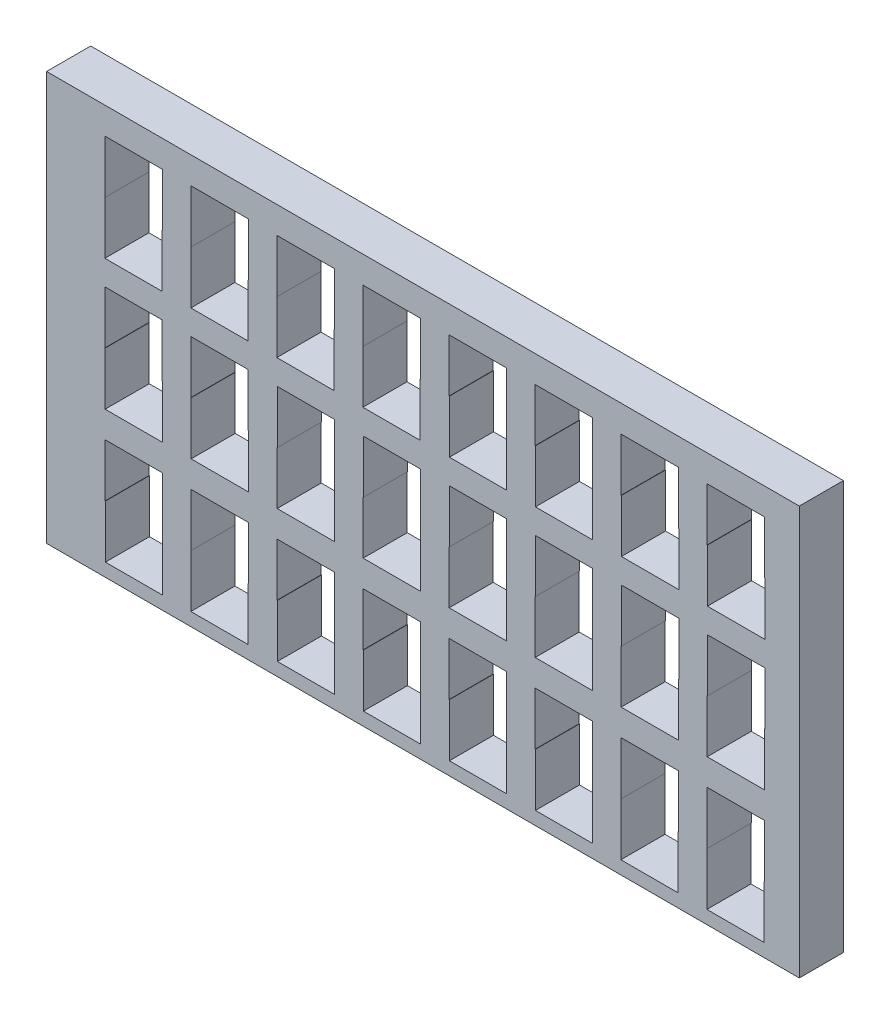
SolidWorks part; units mm, degrees
ref_plane "Front Plane" through (0, 0, 0) normal (0, 0, 1) x (1, 0, 0)
ref_plane "Top Plane" through (0, 0, 0) normal (0, 1, 0) x (1, 0, 0)
ref_plane "Right Plane" through (0, 0, 0) normal (1, 0, 0) x (0, 0, -1)
sketch "Sketch1" plane through (0, 0, 0) normal (0, 0, 1) x (1, 0, 0)
  line L25 (68.6659, 68.7531) -> (68.6659, 56.7531)
  line L26 (68.6659, 68.7531) -> (55.6659, 68.7531)
  line L27 (55.6659, 68.7531) -> (55.6659, 56.7531)
  line L29 (88.1659, 68.7531) -> (88.1659, 56.7531)
  line L30 (88.1659, 68.7531) -> (75.1659, 68.7531)
  line L31 (75.1659, 68.7531) -> (75.1659, 56.7531)
  line L33 (107.6659, 68.7531) -> (107.6659, 56.7531)
  line L35 (94.6659, 68.7531) -> (94.6659, 56.7531)
  line L36 (107.6659, 68.7531) -> (94.6659, 68.7531)
  line L38 (114.1659, 68.7531) -> (114.1659, 56.7531)
  line L39 (127.1659, 68.7531) -> (114.1659, 68.7531)
  line L40 (127.1659, 68.7531) -> (127.1659, 56.7531)
  line L42 (114.2282, 56.7531) -> (114.2282, 44.7531)
  line L46 (127.2282, 44.7531) -> (114.2282, 44.7531)
  line L47 (107.7282, 56.7531) -> (107.7282, 44.7531)
  line L49 (55.7282, 56.7531) -> (55.7282, 44.7531)
  line L50 (68.7282, 44.7531) -> (55.7282, 44.7531)
  line L51 (107.7282, 44.7531) -> (94.7282, 44.7531)
  line L55 (75.2282, 56.7531) -> (75.2282, 44.7531)
  line L59 (68.7282, 56.7531) -> (68.7282, 44.7531)
  line L60 (94.7282, 56.7531) -> (94.7282, 44.7531)
  line L66 (88.2282, 44.7531) -> (75.2282, 44.7531)
  line L67 (127.2282, 56.7531) -> (127.2282, 44.7531)
  line L72 (88.2282, 56.7531) -> (88.2282, 44.7531)
  line L74 (127.2282, 27.1484) -> (127.2282, 39.1484)
  line L75 (127.2282, 39.1484) -> (114.2282, 39.1484)
  line L76 (114.2282, 27.1484) -> (114.2282, 39.1484)
  line L77 (127.1659, 15.1484) -> (127.1659, 27.1484)
  line L78 (127.1659, 15.1484) -> (114.1659, 15.1484)
  line L79 (114.1659, 15.1484) -> (114.1659, 27.1484)
  line L82 (94.7282, 27.1484) -> (94.7282, 39.1484)
  line L83 (107.7282, 39.1484) -> (94.7282, 39.1484)
  line L84 (107.7282, 27.1484) -> (107.7282, 39.1484)
  line L85 (107.6659, 15.1484) -> (94.6659, 15.1484)
  line L86 (94.6659, 15.1484) -> (94.6659, 27.1484)
  line L88 (107.6659, 15.1484) -> (107.6659, 27.1484)
  line L89 (88.2282, 27.1484) -> (88.2282, 39.1484)
  line L90 (88.2282, 39.1484) -> (75.2282, 39.1484)
  line L91 (75.2282, 27.1484) -> (75.2282, 39.1484)
  line L93 (88.1659, 15.1484) -> (75.1659, 15.1484)
  line L94 (75.1659, 15.1484) -> (75.1659, 27.1484)
  line L96 (88.1659, 15.1484) -> (88.1659, 27.1484)
  line L102 (68.7282, 27.1484) -> (68.7282, 39.1484)
  line L103 (68.7282, 39.1484) -> (55.7282, 39.1484)
  line L104 (55.7282, 27.1484) -> (55.7282, 39.1484)
  line L105 (68.6659, 15.1484) -> (55.6659, 15.1484)
  line L106 (55.6659, 15.1484) -> (55.6659, 27.1484)
  line L108 (68.6659, 15.1484) -> (68.6659, 27.1484)
  line L110 (49.2282, 27.1484) -> (49.2282, 39.1484)
  line L111 (36.2282, 39.1484) -> (49.2282, 39.1484)
  line L112 (36.2282, 27.1484) -> (36.2282, 39.1484)
  line L113 (36.1659, 15.1484) -> (36.1659, 27.1484)
  line L114 (36.1659, 15.1484) -> (49.1659, 15.1484)
  line L115 (49.1659, 15.1484) -> (49.1659, 27.1484)
  line L118 (29.7282, 27.1484) -> (29.7282, 39.1484)
  line L119 (16.7282, 39.1484) -> (29.7282, 39.1484)
  line L120 (16.7282, 27.1484) -> (16.7282, 39.1484)
  line L121 (16.6659, 15.1484) -> (16.6659, 27.1484)
  line L122 (16.6659, 15.1484) -> (29.6659, 15.1484)
  line L123 (29.6659, 15.1484) -> (29.6659, 27.1484)
  line L141 (88.1659, 9.1484) -> (88.1659, -2.8516)
  line L143 (75.1659, 9.1484) -> (75.1659, -2.8516)
  line L144 (88.1659, 9.1484) -> (75.1659, 9.1484)
  line L146 (75.2282, -2.8516) -> (75.2282, -14.8516)
  line L147 (88.2282, -14.8516) -> (75.2282, -14.8516)
  line L148 (88.2282, -2.8516) -> (88.2282, -14.8516)
  line L149 (68.6659, 9.1484) -> (68.6659, -2.8516)
  line L151 (55.6659, 9.1484) -> (55.6659, -2.8516)
  line L152 (68.6659, 9.1484) -> (55.6659, 9.1484)
  line L153 (68.7282, -2.8516) -> (68.7282, -14.8516)
  line L154 (68.7282, -14.8516) -> (55.7282, -14.8516)
  line L155 (55.7282, -2.8516) -> (55.7282, -14.8516)
  line L157 (36.1659, 9.1484) -> (49.1659, 9.1484)
  line L158 (49.1659, 9.1484) -> (49.1659, -2.8516)
  line L160 (36.1659, 9.1484) -> (36.1659, -2.8516)
  line L161 (36.2282, -2.8516) -> (36.2282, -14.8516)
  line L162 (36.2282, -14.8516) -> (49.2282, -14.8516)
  line L163 (49.2282, -2.8516) -> (49.2282, -14.8516)
  line L165 (16.6659, 9.1484) -> (29.6659, 9.1484)
  line L166 (29.6659, 9.1484) -> (29.6659, -2.8516)
  line L168 (16.6659, 9.1484) -> (16.6659, -2.8516)
  line L169 (16.7282, -2.8516) -> (16.7282, -14.8516)
  line L170 (16.7282, -14.8516) -> (29.7282, -14.8516)
  line L171 (29.7282, -2.8516) -> (29.7282, -14.8516)
  line L179 (-2.8965, -2.8516) -> (-2.8965, -14.8516)
  line L180 (10.1035, -14.8516) -> (-2.8965, -14.8516)
  line L181 (10.1035, -2.8516) -> (10.1035, -14.8516)
  line L182 (10.1659, 9.1484) -> (10.1659, -2.8516)
  line L184 (-2.8341, 9.1484) -> (-2.8341, -2.8516)
  line L185 (10.1659, 9.1484) -> (-2.8341, 9.1484)
  line L188 (-22.2718, -2.8516) -> (-22.2718, -14.8516)
  line L189 (-22.2718, -14.8516) -> (-9.2718, -14.8516)
  line L190 (-9.2718, -2.8516) -> (-9.2718, -14.8516)
  line L192 (-22.3341, 9.1484) -> (-9.3341, 9.1484)
  line L193 (-9.3341, 9.1484) -> (-9.3341, -2.8516)
  line L195 (-22.3341, 9.1484) -> (-22.3341, -2.8516)
  line L198 (94.6035, -2.8516) -> (94.6035, -14.8516)
  line L199 (94.6035, -14.8516) -> (107.6035, -14.8516)
  line L200 (107.6035, -2.8516) -> (107.6035, -14.8516)
  line L202 (94.6659, 9.1484) -> (107.6659, 9.1484)
  line L203 (107.6659, 9.1484) -> (107.6659, -2.8516)
  line L205 (94.6659, 9.1484) -> (94.6659, -2.8516)
  line L207 (127.1035, -2.8516) -> (127.1035, -14.8516)
  line L208 (114.1035, -14.8516) -> (127.1035, -14.8516)
  line L209 (114.1035, -2.8516) -> (114.1035, -14.8516)
  line L210 (114.1659, 9.1484) -> (127.1659, 9.1484)
  line L211 (127.1659, 9.1484) -> (127.1659, -2.8516)
  line L213 (114.1659, 9.1484) -> (114.1659, -2.8516)
  line L214 (-9.3341, 15.1484) -> (-22.3341, 15.1484)
  line L215 (-22.3341, 15.1484) -> (-22.3341, 27.1484)
  line L217 (-9.3341, 15.1484) -> (-9.3341, 27.1484)
  line L218 (-9.3965, 27.1484) -> (-9.3965, 39.1484)
  line L219 (-9.3965, 39.1484) -> (-22.3965, 39.1484)
  line L220 (-22.3965, 27.1484) -> (-22.3965, 39.1484)
  line L222 (10.1659, 15.1484) -> (-2.8341, 15.1484)
  line L223 (-2.8341, 15.1484) -> (-2.8341, 27.1484)
  line L225 (10.1659, 15.1484) -> (10.1659, 27.1484)
  line L226 (10.1035, 27.1484) -> (10.1035, 39.1484)
  line L227 (10.1035, 39.1484) -> (-2.8965, 39.1484)
  line L228 (-2.8965, 27.1484) -> (-2.8965, 39.1484)
  line L230 (-35.6066, 74.8311) -> (135.0634, 74.8311)
  line L231 (-35.6066, 74.8311) -> (-35.6066, -17.8389)
  line L232 (-35.6066, -17.8389) -> (135.0634, -17.8389)
  line L233 (135.0634, 74.8311) -> (135.0634, -17.8389)
  line L235 (-22.3965, 56.7531) -> (-22.3965, 44.7531)
  line L236 (-22.3965, 44.7531) -> (-9.3965, 44.7531)
  line L237 (-9.3965, 56.7531) -> (-9.3965, 44.7531)
  line L238 (-22.3341, 68.7531) -> (-22.3341, 56.7531)
  line L239 (-22.3341, 68.7531) -> (-9.3341, 68.7531)
  line L240 (-9.3341, 68.7531) -> (-9.3341, 56.7531)
  line L243 (10.1035, 56.7531) -> (10.1035, 44.7531)
  line L244 (-2.8965, 44.7531) -> (10.1035, 44.7531)
  line L245 (-2.8965, 56.7531) -> (-2.8965, 44.7531)
  line L246 (-2.8341, 68.7531) -> (10.1659, 68.7531)
  line L247 (10.1659, 68.7531) -> (10.1659, 56.7531)
  line L249 (-2.8341, 68.7531) -> (-2.8341, 56.7531)
  line L250 (16.6035, 56.7531) -> (16.6035, 44.7531)
  line L251 (16.6035, 44.7531) -> (29.6035, 44.7531)
  line L252 (29.6035, 56.7531) -> (29.6035, 44.7531)
  line L254 (16.6659, 68.7531) -> (29.6659, 68.7531)
  line L255 (29.6659, 68.7531) -> (29.6659, 56.7531)
  line L257 (16.6659, 68.7531) -> (16.6659, 56.7531)
  line L259 (36.1035, 56.7531) -> (36.1035, 44.7531)
  line L260 (36.1035, 44.7531) -> (49.1035, 44.7531)
  line L261 (49.1035, 56.7531) -> (49.1035, 44.7531)
  line L262 (36.1659, 68.7531) -> (49.1659, 68.7531)
  line L263 (49.1659, 68.7531) -> (49.1659, 56.7531)
  line L265 (36.1659, 68.7531) -> (36.1659, 56.7531)
  line L266 (127.2282, 56.7531) -> (114.1659, 56.7531)
  line L267 (107.7282, 56.7531) -> (94.6659, 56.7531)
  line L268 (88.2282, 56.7531) -> (75.1659, 56.7531)
  line L269 (68.7282, 56.7531) -> (55.6659, 56.7531)
  line L270 (49.1659, 56.7531) -> (36.1035, 56.7531)
  line L271 (29.6659, 56.7531) -> (16.6035, 56.7531)
  line L272 (10.1659, 56.7531) -> (-2.8965, 56.7531)
  line L273 (-9.3341, 56.7531) -> (-22.3965, 56.7531)
  line L274 (127.2282, 27.1484) -> (114.1659, 27.1484)
  line L275 (107.7282, 27.1484) -> (94.6659, 27.1484)
  line L276 (88.2282, 27.1484) -> (75.1659, 27.1484)
  line L277 (68.7282, 27.1484) -> (55.6659, 27.1484)
  line L278 (49.2282, 27.1484) -> (36.1659, 27.1484)
  line L279 (29.7282, 27.1484) -> (16.6659, 27.1484)
  line L280 (10.1659, 27.1484) -> (-2.8965, 27.1484)
  line L281 (-9.3341, 27.1484) -> (-22.3965, 27.1484)
  line L282 (127.1659, -2.8516) -> (114.1035, -2.8516)
  line L283 (107.6659, -2.8516) -> (94.6035, -2.8516)
  line L284 (88.2282, -2.8516) -> (75.1659, -2.8516)
  line L285 (68.7282, -2.8516) -> (55.6659, -2.8516)
  line L286 (49.2282, -2.8516) -> (36.1659, -2.8516)
  line L287 (29.7282, -2.8516) -> (16.6659, -2.8516)
  line L288 (10.1659, -2.8516) -> (-2.8965, -2.8516)
  line L289 (-9.2718, -2.8516) -> (-22.3341, -2.8516)
  dimension "D1" = 6.5
  dimension "D10" = 6.5
extrude "Boss-Extrude3" add sketch "Sketch1" along normal blind 10 contours L233 L230 L231 L232 L289 L190 L189 L188 L195 L192 L193 L287 L171 L170 L169 L168 L165 L166 L286 L163 L162 L161 L160 L157 L158 L285 L153 L154 L155 L151 L152 L149 L284 L148 L147 L146 L143 L144 L141 L281
